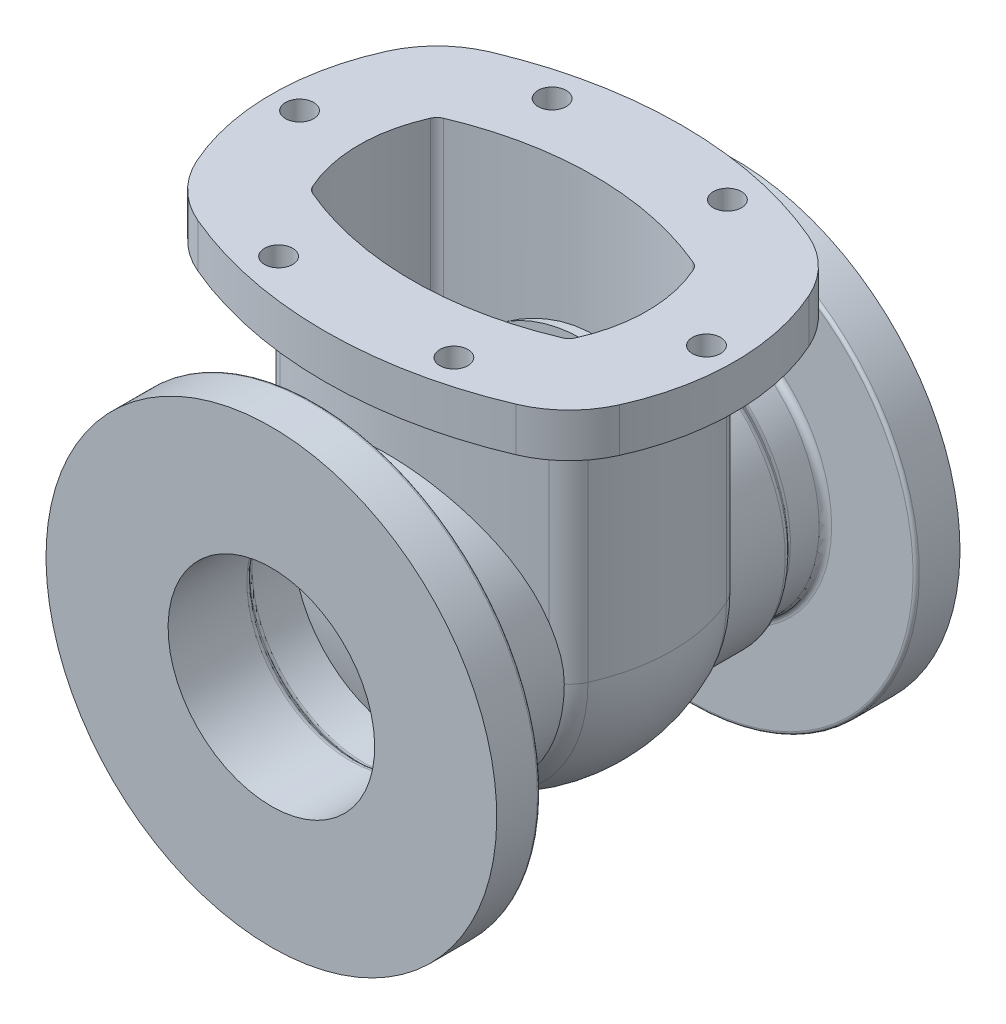
SolidWorks part; units mm, degrees
ref_plane "Front Plane" through (0, 0, 0) normal (0, 0, 1) x (1, 0, 0)
ref_plane "Top Plane" through (0, 0, 0) normal (0, 1, 0) x (1, 0, 0)
ref_plane "Right Plane" through (0, 0, 0) normal (1, 0, 0) x (0, 0, -1)
sketch "Sketch1" plane through (0, 0, 0) normal (1, 0, 0) x (0, 0, -1)
  line L0 (-117.475, 0) -> (117.475, 0) construction
  line L6 (-117.475, -52.3875) -> (-77.5151, -52.3875)
  line L7 (-75.2701, -53.3174) -> (-72.3674, -56.2201)
  line L8 (-70.1224, -57.15) -> (0, -57.15)
  line L9 (-117.475, -52.3875) -> (-117.475, -114.3)
  line L10 (-117.475, -114.3) -> (-96.8375, -114.3)
  line L11 (-95.25, -112.7125) -> (-95.25, -71.4375)
  line L12 (-92.075, -68.2625) -> (-77.5151, -68.2625)
  line L13 (-75.2701, -69.1924) -> (-72.3674, -72.0951)
  line L14 (-70.1224, -73.025) -> (0, -73.025)
  line L15 (0, 0) -> (0, -57.15) construction
  line L32 (70.1224, -73.025) -> (0, -73.025)
  line L33 (75.2701, -69.1924) -> (72.3674, -72.0951)
  line L34 (92.075, -68.2625) -> (77.5151, -68.2625)
  line L35 (95.25, -112.7125) -> (95.25, -71.4375)
  line L36 (117.475, -114.3) -> (96.8375, -114.3)
  line L37 (117.475, -52.3875) -> (117.475, -114.3)
  line L38 (70.1224, -57.15) -> (0, -57.15)
  line L39 (75.2701, -53.3174) -> (72.3674, -56.2201)
  line L40 (117.475, -52.3875) -> (77.5151, -52.3875)
  line L41 (-41.275, -57.15) -> (-41.275, -73.025)
  line L42 (41.275, -57.15) -> (41.275, -73.025)
  arc A10 (-95.25, -112.7125) -> (-96.8375, -114.3) centre (-96.8375, -112.7125) cw
  arc A12 (-70.1224, -57.15) -> (-72.3674, -56.2201) centre (-70.1224, -53.975) cw
  arc A13 (-77.5151, -52.3875) -> (-75.2701, -53.3174) centre (-77.5151, -55.5625) cw
  arc A14 (-70.1224, -73.025) -> (-72.3674, -72.0951) centre (-70.1224, -69.85) cw
  arc A15 (-75.2701, -69.1924) -> (-77.5151, -68.2625) centre (-77.5151, -71.4375) ccw
  arc A16 (-92.075, -68.2625) -> (-95.25, -71.4375) centre (-92.075, -71.4375) ccw
  arc A17 (95.25, -71.4375) -> (92.075, -68.2625) centre (92.075, -71.4375) ccw
  arc A18 (75.2701, -53.3174) -> (77.5151, -52.3875) centre (77.5151, -55.5625) cw
  arc A19 (72.3674, -56.2201) -> (70.1224, -57.15) centre (70.1224, -53.975) cw
  arc A20 (75.2701, -69.1924) -> (77.5151, -68.2625) centre (77.5151, -71.4375) cw
  arc A21 (72.3674, -72.0951) -> (70.1224, -73.025) centre (70.1224, -69.85) cw
  arc A23 (96.8375, -114.3) -> (95.25, -112.7125) centre (96.8375, -112.7125) cw
  point P3 (0, 0)
  point P6 (-41.023, -73.025)
  point P40 (-95.25, -114.3)
  point P46 (-71.4375, -57.15)
  point P49 (-76.2, -52.3875)
  point P52 (-71.4375, -73.025)
  point P55 (-76.2, -68.2625)
  point P58 (-95.25, -68.2625)
  point P61 (95.25, -68.2625)
  point P64 (76.2, -52.3875)
  point P67 (71.4375, -57.15)
  point P70 (76.2, -68.2625)
  point P73 (71.4375, -73.025)
  point P79 (95.25, -114.3)
  dimension "D14" = 1.5875
  dimension "D15" = 3.175
  dimension "D20" = 3.175
  dimension "D21" = 1.5875
  dimension "D1" = 234.95
  dimension "D2" = 41.275
  dimension "D3" = 52.3875
  dimension "D4" = 4.7625
  dimension "D5" = 45
  dimension "D6" = 22.225
  dimension "D7" = 15.875
  dimension "D8" = 114.3
  dimension "D9" = 4.7625
  dimension "D10" = 19.05
  dimension "D11" = 71.4375
  dimension "D12" = 76.2
revolve "Revolve1" add sketch "Sketch1" angle 360 about L0
ref_plane "Plane2" through (0, 142.875, 0) normal (0, 1, 0) x (1, 0, 0)
sketch "Sketch6" plane through (0, 142.875, 0) normal (0, 1, 0) x (1, 0, 0)
  line L0 (-114.3, 0) -> (114.3, 0) construction
  line L1 (0, -117.475) -> (0, 117.475) construction
  line L2 (-114.3, -117.475) -> (114.3, -117.475) construction
  line L3 (114.3, 117.475) -> (-114.3, 117.475) construction
  arc A0 (63.3113, 33.1473) -> (-63.3113, 33.1473) centre (0, -115.8875) ccw
  arc A1 (-66.6217, -29.9031) -> (-66.6217, 29.9031) centre (0, 0) cw
  arc A2 (-66.6217, 29.9031) -> (-63.3113, 33.1473) centre (-60.8285, 27.3028) cw
  arc A3 (-107.1741, -48.105) -> (-107.1741, 48.105) centre (0, 0) cw
  arc A4 (-107.1741, 48.105) -> (-80.6909, 74.0588) centre (-60.8285, 27.3028) cw
  arc A5 (80.6909, 74.0588) -> (-80.6909, 74.0588) centre (0, -115.8875) ccw
  arc A6 (-66.6217, -29.9031) -> (-63.3113, -33.1473) centre (-60.8285, -27.3028) ccw
  arc A7 (63.3113, -33.1473) -> (-63.3113, -33.1473) centre (0, 115.8875) cw
  arc A8 (80.6909, -74.0588) -> (-80.6909, -74.0588) centre (0, 115.8875) cw
  arc A9 (-107.1741, -48.105) -> (-80.6909, -74.0588) centre (-60.8285, -27.3028) ccw
  arc A10 (107.1741, 48.105) -> (80.6909, 74.0588) centre (60.8285, 27.3028) ccw
  arc A11 (66.6217, -29.9031) -> (66.6217, 29.9031) centre (0, 0) ccw
  arc A12 (107.1741, -48.105) -> (107.1741, 48.105) centre (0, 0) ccw
  arc A13 (107.1741, -48.105) -> (80.6909, -74.0588) centre (60.8285, -27.3028) cw
  arc A14 (66.6217, 29.9031) -> (63.3113, 33.1473) centre (60.8285, 27.3028) ccw
  arc A15 (66.6217, -29.9031) -> (63.3113, -33.1473) centre (60.8285, -27.3028) cw
  arc A16 (44.45, 69.3541) -> (-44.45, 69.3541) centre (0, -115.8875) ccw
  circle A17 centre (-44.45, 69.3541) radius 7.1438
  circle A18 centre (44.45, 69.3541) radius 7.1438
  circle A19 centre (-44.45, -69.3541) radius 7.1438
  circle A20 centre (44.45, -69.3541) radius 7.1438
  arc A21 (44.45, -69.3541) -> (-44.45, -69.3541) centre (0, 115.8875) cw
  circle A22 centre (103.1875, 0) radius 7.1438
  circle A23 centre (-103.1875, 0) radius 7.1438
  dimension "D1" = 115.8875
  dimension "D2" = 161.925
  dimension "D3" = 73.025
  dimension "D5" = 117.475
  dimension "D6" = 206.375
  dimension "D7" = 190.5
  dimension "D4" = 6.35
  dimension "D8" = 14.2875
  dimension "D10" = 103.1875
  dimension "D9" = 44.45
extrude "Boss-Extrude1" add sketch "Sketch6" against normal blind 22.225 separate body
sketch "Sketch7" plane through (0, 120.65, 0) normal (0, -1, 0) x (1, 0, 0)
  arc A0 (-63.3113, 33.1473) -> (-66.6217, 29.9031) centre (-60.8285, 27.3028) ccw construction
  arc A1 (-66.6217, 29.9031) -> (-66.6217, -29.9031) centre (0, 0) ccw construction
  arc A2 (-66.6217, -29.9031) -> (-63.3113, -33.1473) centre (-60.8285, -27.3028) ccw construction
  arc A3 (-63.3113, -33.1473) -> (63.3113, -33.1473) centre (0, 115.8875) ccw construction
  arc A4 (63.3113, -33.1473) -> (66.6217, -29.9031) centre (60.8285, -27.3028) ccw construction
  arc A5 (66.6217, 29.9031) -> (63.3113, 33.1473) centre (60.8285, 27.3028) ccw construction
  arc A6 (63.3113, 33.1473) -> (-63.3113, 33.1473) centre (0, -115.8875) ccw construction
  arc A7 (66.6217, -29.9031) -> (66.6217, 29.9031) centre (0, 0) ccw construction
  arc A8 (-63.3113, 33.1473) -> (-66.6217, 29.9031) centre (-60.8285, 27.3028) ccw
  arc A9 (-66.6217, 29.9031) -> (-66.6217, -29.9031) centre (0, 0) ccw
  arc A10 (-66.6217, -29.9031) -> (-63.3113, -33.1473) centre (-60.8285, -27.3028) ccw
  arc A11 (-63.3113, -33.1473) -> (63.3113, -33.1473) centre (0, 115.8875) ccw
  arc A12 (63.3113, -33.1473) -> (66.6217, -29.9031) centre (60.8285, -27.3028) ccw
  arc A13 (66.6217, 29.9031) -> (63.3113, 33.1473) centre (60.8285, 27.3028) ccw
  arc A14 (63.3113, 33.1473) -> (-63.3113, 33.1473) centre (0, -115.8875) ccw
  arc A15 (66.6217, -29.9031) -> (66.6217, 29.9031) centre (0, 0) ccw
  arc A16 (68.2769, 44.8363) -> (-68.2769, 44.8363) centre (0, -115.8875) ccw
  arc A17 (-68.2769, 44.8363) -> (-78.2081, 35.1036) centre (-60.8285, 27.3028) ccw
  arc A18 (-78.2081, 35.1036) -> (-78.2081, -35.1036) centre (0, 0) ccw
  arc A19 (-78.2081, -35.1036) -> (-68.2769, -44.8363) centre (-60.8285, -27.3028) ccw
  arc A20 (-68.2769, -44.8363) -> (68.2769, -44.8363) centre (0, 115.8875) ccw
  arc A21 (68.2769, -44.8363) -> (78.2081, -35.1036) centre (60.8285, -27.3028) ccw
  arc A22 (78.2081, -35.1036) -> (78.2081, 35.1036) centre (0, 0) ccw
  arc A23 (78.2081, 35.1036) -> (68.2769, 44.8363) centre (60.8285, 27.3028) ccw
  dimension "D1" = 12.7
extrude "Boss-Extrude4" add sketch "Sketch7" along normal blind 120.65
sketch "Sketch11" plane through (0, 0, 0) normal (0, -1, 0) x (1, 0, 0)
  line L0 (0, 58.7375) -> (0, -58.7375) construction
  arc A0 (68.2769, 44.8363) -> (-68.2769, 44.8363) centre (0, -115.8875) ccw construction
  arc A1 (-68.2769, -44.8363) -> (68.2769, -44.8363) centre (0, 115.8875) ccw construction
  arc A2 (68.2769, 44.8363) -> (0, 58.7375) centre (0, -115.8875) ccw
  arc A3 (0, -58.7375) -> (68.2769, -44.8363) centre (0, 115.8875) ccw
  arc A10 (-63.3113, 33.1473) -> (-66.6217, 29.9031) centre (-60.8285, 27.3028) ccw
  arc A11 (63.3113, 33.1473) -> (-63.3113, 33.1473) centre (0, -115.8875) ccw
  arc A12 (66.6217, 29.9031) -> (63.3113, 33.1473) centre (60.8285, 27.3028) ccw
  arc A13 (66.6217, -29.9031) -> (66.6217, 29.9031) centre (0, 0) ccw
  arc A14 (63.3113, -33.1473) -> (66.6217, -29.9031) centre (60.8285, -27.3028) ccw
  arc A15 (-63.3113, -33.1473) -> (63.3113, -33.1473) centre (0, 115.8875) ccw
  arc A16 (-66.6217, -29.9031) -> (-63.3113, -33.1473) centre (-60.8285, -27.3028) ccw
  arc A17 (-66.6217, 29.9031) -> (-66.6217, -29.9031) centre (0, 0) ccw
  arc A19 (63.3113, 33.1473) -> (0, 46.0375) centre (0, -115.8875) ccw
  arc A20 (66.6217, 29.9031) -> (63.3113, 33.1473) centre (60.8285, 27.3028) ccw
  arc A21 (66.6217, -29.9031) -> (66.6217, 29.9031) centre (0, 0) ccw
  arc A22 (63.3113, -33.1473) -> (66.6217, -29.9031) centre (60.8285, -27.3028) ccw
  arc A23 (0, -46.0375) -> (63.3113, -33.1473) centre (0, 115.8875) ccw
  dimension "D1" = 0
revolve "Revolve3" add sketch "Sketch11" angle 180 about L0
